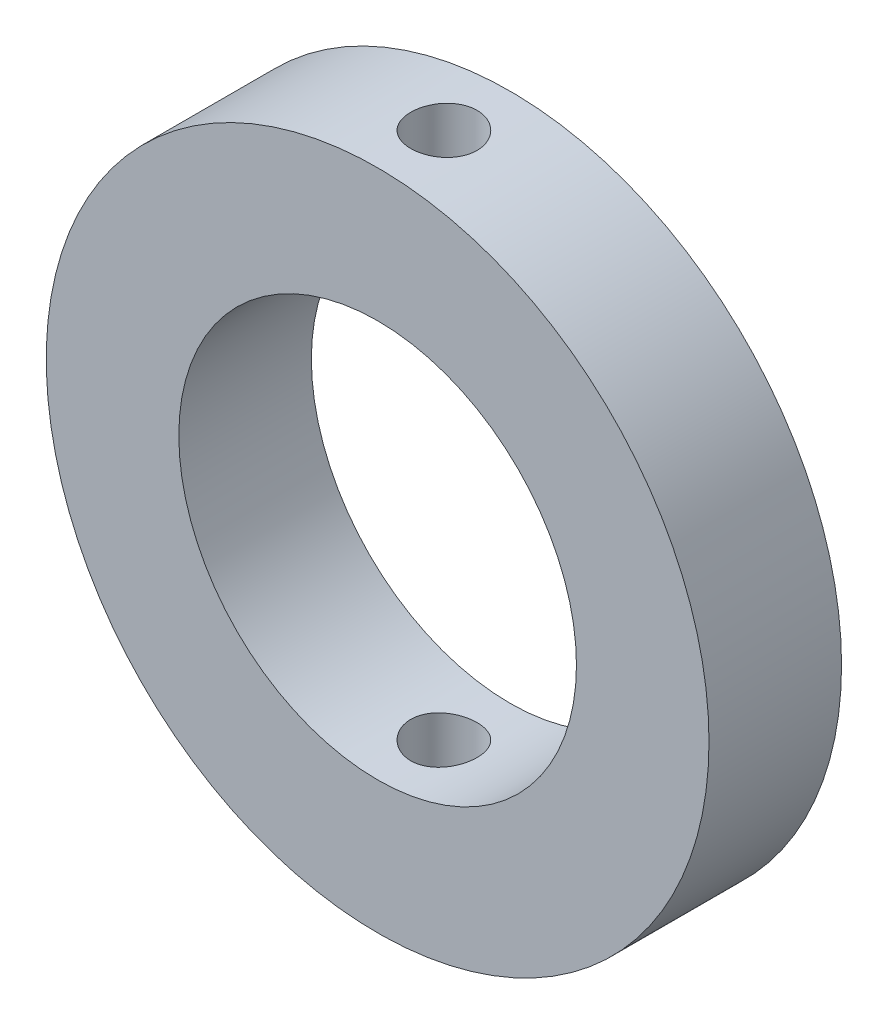
SolidWorks part; units mm, degrees
ref_plane "Front Plane" through (0, 0, 0) normal (0, 0, 1) x (1, 0, 0)
ref_plane "Top Plane" through (0, 0, 0) normal (0, 1, 0) x (1, 0, 0)
ref_plane "Right Plane" through (0, 0, 0) normal (1, 0, 0) x (0, 0, -1)
sketch "Sketch1" plane through (0, 0, 0) normal (0, 0, 1) x (1, 0, 0)
  circle A0 centre (0, 0) radius 25
  circle A1 centre (0, 0) radius 15
  dimension "D1" = 50
  dimension "D2" = 30
extrude "Boss-Extrude1" add sketch "Sketch1" along normal blind 10
sketch "Sketch2" plane through (0, 0, 0) normal (0, 1, 0) x (1, 0, 0)
  circle A0 centre (0, -5) radius 2.5
  dimension "D1" = 5
  dimension "D2" = 5
extrude "Cut-Extrude1" cut sketch "Sketch2" against normal mid plane 75
